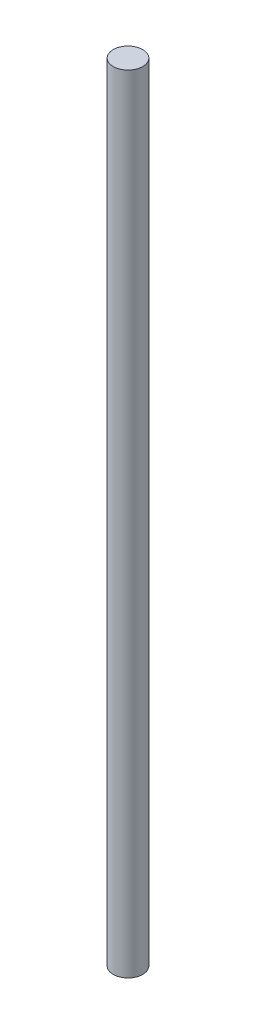
SolidWorks part; units mm, degrees
ref_plane "Front Plane" through (0, 0, 0) normal (0, 0, 1) x (1, 0, 0)
ref_plane "Top Plane" through (0, 0, 0) normal (0, 1, 0) x (1, 0, 0)
ref_plane "Right Plane" through (0, 0, 0) normal (1, 0, 0) x (0, 0, -1)
sketch "Sketch1" plane through (0, 0, 0) normal (0, 1, 0) x (1, 0, 0)
  circle A0 centre (0, 0) radius 4.7625
  dimension "D1" = 9.525
extrude "Boss-Extrude1" add sketch "Sketch1" along normal blind 254
